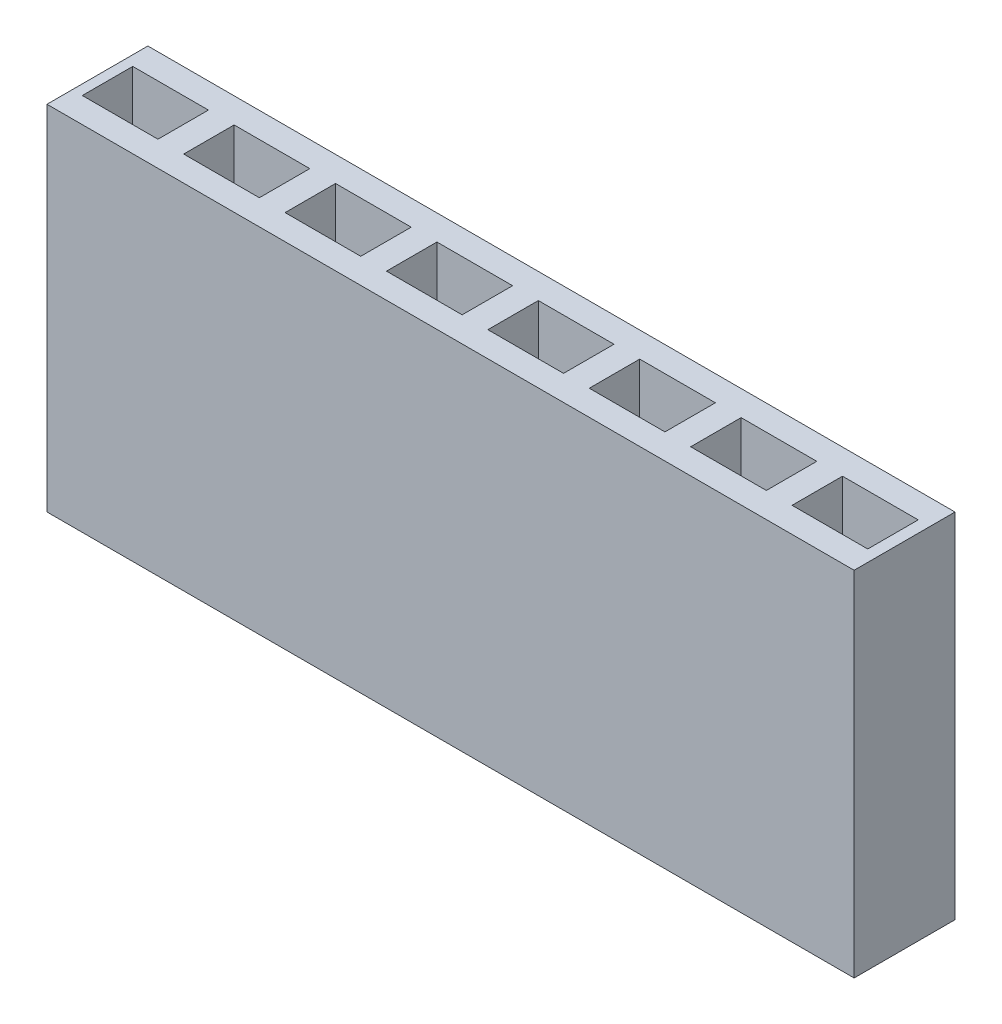
SolidWorks part; units mm, degrees
ref_plane "Front Plane" through (0, 0, 0) normal (0, 0, 1) x (1, 0, 0)
ref_plane "Top Plane" through (0, 0, 0) normal (0, 1, 0) x (1, 0, 0)
ref_plane "Right Plane" through (0, 0, 0) normal (1, 0, 0) x (0, 0, -1)
sketch "Sketch1" plane through (0, 0, 0) normal (0, 0, 1) x (1, 0, 0)
  line L1 (0, 0) -> (16, 0)
  line L2 (0, 0) -> (0, 7)
  line L3 (0, 7) -> (16, 7)
  line L4 (16, 0) -> (16, 7)
  dimension "D1" = 7
  dimension "D2" = 16
extrude "Boss-Extrude1" add sketch "Sketch1" along normal blind 2
sketch "Sketch2" plane through (0, 7, 0) normal (0, 1, 0) x (1, 0, 0)
  line L0 (0, -1) -> (16, -1) construction
  line L1 (0, -2) -> (0, 0) construction
  line L2 (16, -2) -> (16, 0) construction
  line L4 (0.2, -0.5) -> (1.7, -0.5)
  line L5 (0.2, -0.5) -> (0.2, -1.5)
  line L6 (0.2, -1.5) -> (1.7, -1.5)
  line L7 (1.7, -0.5) -> (1.7, -1.5)
  dimension "D1" = 0.2
  dimension "D2" = 1.5
  dimension "D3" = 1
extrude "Cut-Extrude1" cut sketch "Sketch2" against normal blind 4
pattern_linear "LPattern1" count 8 spacing 2.01 along (1, 0, 0) of "Cut-Extrude1"
